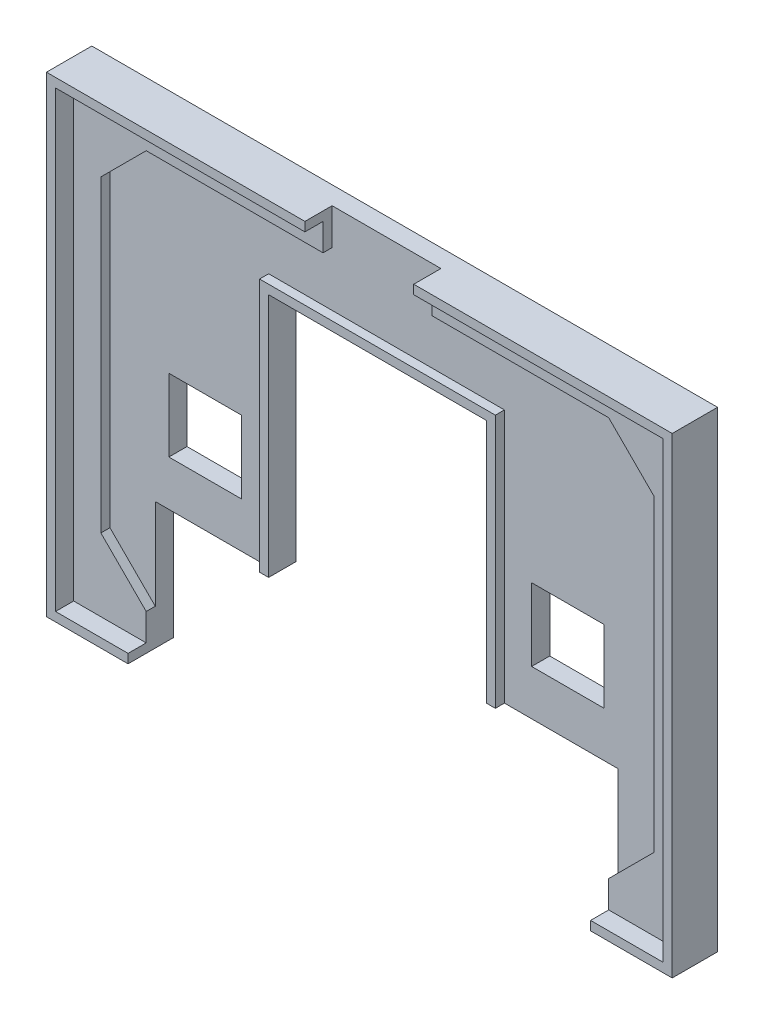
SolidWorks part; units mm, degrees
ref_plane "Přední rovina" through (0, 0, 0) normal (0, 0, 1) x (1, 0, 0)
ref_plane "Horní rovina" through (0, 0, 0) normal (0, 1, 0) x (1, 0, 0)
ref_plane "Pravá rovina" through (0, 0, 0) normal (1, 0, 0) x (0, 0, -1)
sketch "Skica1" plane through (0, 0, 0) normal (0, 0, 1) x (1, 0, 0)
  line L1 (-33.5, -25) -> (33.5, -25)
  line L2 (-33.5, -25) -> (-33.5, 25)
  line L3 (-33.5, 25) -> (33.5, 25)
  line L4 (33.5, -25) -> (33.5, 25)
  line L5 (-33.5, -25) -> (33.5, 25) construction
  line L6 (-33.5, 25) -> (33.5, -25) construction
  point P0 (0, 0)
  dimension "D1" = 67
  dimension "D2" = 50
extrude "Přidat vysunutím1" add sketch "Skica1" along normal blind 3
sketch "Skica2" plane through (0, 0, 3) normal (0, 0, 1) x (1, 0, 0)
  line L0 (-1000, 0) -> (49000, 0) construction
  line L1 (0, -1000) -> (0, 49000) construction
  line L2 (-1000, -22) -> (49000, -22) construction
  line L3 (-25.5, -1000) -> (-25.5, 49000) construction
  line L4 (-30.5, -1000) -> (-30.5, 49000) construction
  line L6 (-33.5, -25) -> (33.5, -25) construction
  line L7 (-25.5, -22) -> (-30.5, -17)
  line L8 (-30.5, -17) -> (-30.5, 17)
  line L9 (-25.5, -22) -> (25.5, -22)
  line L10 (30.5, -17) -> (30.5, 17)
  line L11 (25.5, -22) -> (30.5, -17)
  line L12 (25.5, 22) -> (30.5, 17)
  line L13 (-25.5, 22) -> (25.5, 22)
  line L14 (-25.5, 22) -> (-30.5, 17)
  point P20 (0, -22)
  point P21 (30.5, 0)
  point P24 (-30.5, 0)
  dimension "D1" = 30.5
  dimension "D2" = 5
  dimension "D3" = 3
  dimension "D4" = 45
extrude "Odebrat vysunutím1" cut sketch "Skica2" against normal offset from surface (1 mm away) 2 up to face at (0, 0, 0)
sketch "Skica3" plane through (0, 0, 0) normal (0, 0, -1) x (-1, 0, 0)
  line L0 (0, -1000) -> (0, 49000) construction
  line L1 (33.5, -25) -> (-33.5, -25) construction
  line L2 (24, 1) -> (16, 1)
  line L3 (24, 1) -> (24, -7)
  line L4 (24, -7) -> (16, -7)
  line L5 (16, 1) -> (16, -7)
  line L6 (-16, 1) -> (-16, -7)
  line L7 (33.5, -25) -> (-33.5, -25) construction
  line L8 (25.5, -25) -> (-25.5, -25)
  line L9 (25.5, -25) -> (25.5, -12)
  line L11 (-25.5, -25) -> (-25.5, -12)
  line L12 (-24, -7) -> (-16, -7)
  line L13 (25.5, -12) -> (12, -12)
  line L15 (12, -12) -> (12, 15)
  line L16 (12, 15) -> (-12, 15)
  line L17 (-12, -12) -> (-12, 15)
  line L18 (-12, -12) -> (-25.5, -12)
  line L19 (-24, 1) -> (-24, -7)
  line L20 (-24, 1) -> (-16, 1)
  dimension "D1" = 16
  dimension "D2" = 8
  dimension "D3" = 18
  dimension "D4" = 13
  dimension "D5" = 51
  dimension "D6" = 24
  dimension "D7" = 27
extrude "Odebrat vysunutím2" cut sketch "Skica3" against normal through all
sketch "Skica4" plane through (0, 0, 2) normal (0, 0, 1) x (1, 0, 0)
  line L0 (12, 15) -> (12, -12) construction
  line L1 (-12, -12) -> (-12, 15) construction
  line L2 (-12, 15) -> (12, 15) construction
  line L3 (12, 15) -> (12, -12)
  line L4 (-12, -12) -> (-12, 15)
  line L5 (-12, 15) -> (12, 15)
extrude "Vysunout tenkostěnný1" add sketch "Skica4" along normal up to surface (1 mm away) thin up to face at (0, -3.5714, 3) thin type one direction reverse wall 1
sketch "Skica5" plane through (0, 0, 0) normal (0, 0, -1) x (-1, 0, 0)
  line L0 (-33.5, 25) -> (33.5, 25) construction
  line L1 (33.5, 25) -> (33.5, -25) construction
  line L2 (33.5, -25) -> (25.5, -25) construction
  line L3 (-33.5, -25) -> (-33.5, 25) construction
  line L4 (-25.5, -25) -> (-33.5, -25) construction
  line L5 (-33.5, 25) -> (33.5, 25)
  line L6 (33.5, 25) -> (33.5, -25)
  line L7 (33.5, -25) -> (25.5, -25)
  line L8 (-33.5, -25) -> (-33.5, 25)
  line L9 (-25.5, -25) -> (-33.5, -25)
extrude "Vysunout tenkostěnný2" add sketch "Skica5" against normal blind 5 thin thin type one direction reverse wall 1
sketch "Skica6" plane through (0, 0, 2) normal (0, 0, 1) x (1, 0, 0)
  line L0 (0, -1000) -> (0, 49000) construction
  line L1 (25.5, 22) -> (-25.5, 22) construction
  line L2 (-6, 22) -> (6, 22)
  line L3 (-6, 22) -> (-6, 26)
  line L4 (-6, 26) -> (6, 26)
  line L5 (6, 22) -> (6, 26)
  line L6 (34.5, 26) -> (-34.5, 26) construction
  dimension "D1" = 12
extrude "Odebrat vysunutím3" cut sketch "Skica6" along normal through all
sketch "Skica7" plane through (0, 0, 0) normal (0, 0, -1) x (-1, 0, 0)
  line L0 (-412.4785, -204.4844) -> (-71.1451, -204.4844) construction
  line L1 (-32.44, 14.5405) -> (-23.4595, 23.94)
  line L2 (-23.4595, 23.94) -> (-14.06, 14.9595)
  line L3 (-14.06, 14.9595) -> (-23.0405, 5.56)
  line L4 (-23.0405, 5.56) -> (-32.44, 14.5405)
  line L5 (-34.5, 26) -> (34.5, 26) construction
  line L6 (0, 0) -> (0, 28.27) construction
  line L7 (-34.5, -26) -> (-34.5, 26) construction
  line L8 (14.06, 14.9595) -> (23.0405, 5.56)
  line L9 (23.4595, 23.94) -> (14.06, 14.9595)
  line L10 (32.44, 14.5405) -> (23.4595, 23.94)
  line L11 (23.0405, 5.56) -> (32.44, 14.5405)
  dimension "D1" = 13
  dimension "D2" = 13
  dimension "D3" = 2.06
  dimension "D4" = 2.06
  dimension "D5" = 2.06
extrude "Odebrat vysunutím5" cut sketch "Skica7" against normal blind 1
sketch "Skica8" plane through (0, 0, 0) normal (0, 0, -1) x (-1, 0, 0)
  line L0 (-29.2669, 14.9665) -> (-27.4593, 13.2395)
  line L1 (-27.4593, 13.2395) -> (-25.7669, 15.0108)
  line L4 (-32.44, 14.5405) -> (-23.0405, 5.56) construction
  line L5 (-23.4595, 23.94) -> (-32.44, 14.5405) construction
  line L7 (-23.6268, 17.2508) -> (-21.9329, 19.0238)
  line L8 (-21.9329, 19.0238) -> (-23.7405, 20.7508)
  line L10 (-14.06, 14.9595) -> (-23.4595, 23.94) construction
  line L12 (-24.551, 9.7693) -> (-26.3586, 11.4963)
  line L13 (-26.3586, 11.4963) -> (-25.6678, 12.2194)
  line L15 (-20.1414, 18.0037) -> (-18.3338, 16.2767)
  line L16 (-32.44, 14.5405) -> (-23.0405, 5.56) construction
  line L17 (0, 0) -> (0, 27.7759) construction
  line L30 (-29.2669, 14.9665) -> (-25.7669, 15.0108)
  line L34 (-23.9408, 14.027) -> (-22.5592, 15.473)
  line L37 (-20.8322, 17.2806) -> (-20.1414, 18.0037)
  line L38 (-24.551, 9.7693) -> (-22.1332, 12.2999)
  line L39 (-22.1332, 12.2999) -> (-22.3041, 13.8463)
  line L40 (-22.3041, 13.8463) -> (-20.7516, 13.746)
  line L41 (-20.7516, 13.746) -> (-18.3338, 16.2767)
  line L42 (-25.6678, 12.2194) -> (-23.9408, 12.2194)
  line L43 (-23.9408, 12.2194) -> (-23.9408, 14.027)
  line L45 (-20.8322, 15.473) -> (-20.8322, 17.2806)
  line L46 (-22.5592, 15.473) -> (-20.8322, 15.473)
  line L47 (-23.6268, 17.2508) -> (-23.7405, 20.7508)
  line L48 (27.4593, 13.2395) -> (25.7669, 15.0108)
  line L49 (29.2669, 14.9665) -> (27.4593, 13.2395)
  line L50 (29.2669, 14.9665) -> (25.7669, 15.0108)
  line L51 (23.6268, 17.2508) -> (21.9329, 19.0238)
  line L52 (21.9329, 19.0238) -> (23.7405, 20.7508)
  line L53 (23.6268, 17.2508) -> (23.7405, 20.7508)
  line L54 (23.9408, 14.027) -> (22.5592, 15.473)
  line L55 (23.9408, 12.2194) -> (23.9408, 14.027)
  line L56 (25.6678, 12.2194) -> (23.9408, 12.2194)
  line L57 (26.3586, 11.4963) -> (25.6678, 12.2194)
  line L58 (24.551, 9.7693) -> (26.3586, 11.4963)
  line L59 (24.551, 9.7693) -> (22.1332, 12.2999)
  line L60 (22.1332, 12.2999) -> (22.3041, 13.8463)
  line L61 (22.3041, 13.8463) -> (20.7516, 13.746)
  line L62 (20.7516, 13.746) -> (18.3338, 16.2767)
  line L63 (20.1414, 18.0037) -> (18.3338, 16.2767)
  line L64 (20.8322, 17.2806) -> (20.1414, 18.0037)
  line L65 (20.8322, 15.473) -> (20.8322, 17.2806)
  line L66 (22.5592, 15.473) -> (20.8322, 15.473)
  point P22 (-18.7598, 19.4498)
  dimension "2,5" = 2.5
  dimension "D2" = 2.5
  dimension "D3" = 2
  dimension "D4" = 1
  dimension "D5" = 1
  dimension "D6" = 2
  dimension "D7" = 2.5
  dimension "D8" = 2.5
  dimension "D9" = 3.5
  dimension "D10" = 2.5
  dimension "D11" = 2.5
  dimension "D12" = 2
  dimension "D13" = 2
  dimension "D14" = 2
  dimension "D15" = 2
  dimension "D16" = 3.5
  dimension "D17" = 40
  dimension "D18" = 40
  dimension "D19" = 2.5
  dimension "D20" = 90
  dimension "D21" = 90
  dimension "D22" = 3.5
  dimension "D23" = 3.5
  dimension "D24" = 2.5
  dimension "D25" = 2.5
  dimension "D26" = 3.098
extrude "Přidat vysunutím3" add sketch "Skica8" along normal blind 1 from offset 1 offset against normal yes
sketch "Skica9" plane through (0, 0, 0) normal (0, 0, -1) x (-1, 0, 0)
  line L0 (-10.3, 23.3) -> (-7.1, 23.3)
  line L1 (-7.1, 23.3) -> (-7.1, 22.5)
  line L2 (-7.1, 22.5) -> (-6.3, 22.5)
  line L3 (-6.3, 22.5) -> (-6.3, 21.7)
  line L4 (-6.3, 21.7) -> (-7.9, 21.7)
  line L5 (-7.9, 21.7) -> (-7.9, 22.5)
  line L6 (-7.9, 22.5) -> (-9.5, 22.5)
  line L7 (-9.5, 22.5) -> (-9.5, 18.5)
  line L8 (-9.5, 18.5) -> (-7.9, 18.5)
  line L9 (-7.9, 18.5) -> (-7.9, 19.3)
  line L10 (-7.9, 19.3) -> (-8.7, 19.3)
  line L11 (-8.7, 19.3) -> (-8.7, 20.1)
  line L12 (-8.7, 20.1) -> (-6.3, 20.1)
  line L13 (-6.3, 20.1) -> (-6.3, 18.5)
  line L14 (-6.3, 18.5) -> (-7.1, 18.5)
  line L15 (-7.1, 18.5) -> (-7.1, 17.7)
  line L16 (-7.1, 17.7) -> (-10.3, 17.7)
  line L17 (-10.3, 17.7) -> (-10.3, 18.5)
  line L18 (-10.3, 18.5) -> (-11.1, 18.5)
  line L19 (-11.1, 18.5) -> (-11.1, 22.5)
  line L20 (-11.1, 22.5) -> (-10.3, 22.5)
  line L21 (-10.3, 22.5) -> (-10.3, 23.3)
  line L22 (-5.3, 23.3) -> (-1.3, 23.3)
  line L23 (-1.3, 23.3) -> (-1.3, 22.3)
  line L24 (-1.3, 22.3) -> (-4, 22.3)
  line L25 (-4, 22.3) -> (-4, 21)
  line L26 (-4, 21) -> (-2.4, 21)
  line L27 (-2.4, 21) -> (-2.4, 20)
  line L28 (-2.4, 20) -> (-4, 20)
  line L29 (-4, 20) -> (-4, 18.7)
  line L30 (-4, 18.7) -> (-1.3, 18.7)
  line L31 (-1.3, 18.7) -> (-1.3, 17.7)
  line L32 (-1.3, 17.7) -> (-5.3, 17.7)
  line L33 (-5.3, 17.7) -> (-5.3, 23.3)
  line L34 (-0.3, 23.3) -> (1.3, 23.3)
  line L35 (1.3, 23.3) -> (1.3, 22.5)
  line L36 (1.3, 22.5) -> (2.1, 22.5)
  line L37 (2.1, 22.5) -> (2.1, 21.7)
  line L38 (2.1, 21.7) -> (2.9, 21.7)
  line L39 (2.9, 21.7) -> (2.9, 22.5)
  line L40 (2.9, 22.5) -> (3.7, 22.5)
  line L43 (5.3, 23.3) -> (5.3, 17.7)
  line L44 (5.3, 17.7) -> (3.7, 17.7)
  line L45 (3.7, 17.7) -> (3.7, 20.7)
  line L46 (3.7, 20.7) -> (2.9, 20.7)
  line L47 (2.9, 20.7) -> (2.9, 19.9)
  line L48 (2.9, 19.9) -> (2.1, 19.9)
  line L49 (2.1, 19.9) -> (2.1, 20.7)
  line L50 (2.1, 20.7) -> (1.3, 20.7)
  line L51 (1.3, 20.7) -> (1.3, 17.7)
  line L52 (1.3, 17.7) -> (-0.3, 17.7)
  line L53 (-0.3, 17.7) -> (-0.3, 23.3)
  line L54 (7.1, 23.3) -> (10.3, 23.3)
  line L55 (10.3, 23.3) -> (10.3, 22.5)
  line L56 (10.3, 22.5) -> (11.1, 22.5)
  line L57 (11.1, 22.5) -> (11.1, 18.5)
  line L58 (11.1, 18.5) -> (10.3, 18.5)
  line L59 (10.3, 18.5) -> (10.3, 17.7)
  line L60 (10.3, 17.7) -> (7.1, 17.7)
  line L61 (7.1, 17.7) -> (7.1, 18.5)
  line L62 (7.1, 18.5) -> (6.3, 18.5)
  line L63 (6.3, 18.5) -> (6.3, 22.5)
  line L64 (6.3, 22.5) -> (7.1, 22.5)
  line L65 (7.1, 22.5) -> (7.1, 23.3)
  line L66 (-12, 15) -> (-12, -12) construction
  line L67 (-34.5, 26) -> (34.5, 26) construction
  line L69 (3.7, 22.5) -> (3.7, 23.3)
  line L70 (3.7, 23.3) -> (5.3, 23.3)
  dimension "D1" = 3.2
  dimension "D2" = 0.8
  dimension "D3" = 0.8
  dimension "D4" = 0.8
  dimension "D5" = 0.8
  dimension "D6" = 0.8
  dimension "D7" = 5.6
  dimension "D8" = 0.8
  dimension "D9" = 0.8
  dimension "D10" = 3.2
  dimension "D11" = 0.8
  dimension "D12" = 0.8
  dimension "D13" = 1.6
  dimension "D14" = 0.8
  dimension "D15" = 2.4
  dimension "D16" = 0.8
  dimension "D17" = 0.8
  dimension "D18" = 0.9
  dimension "D19" = 2.7
  dimension "D20" = 1.6
  dimension "D21" = 0.8
  dimension "D22" = 1.6
  dimension "D23" = 4
  dimension "D24" = 4
  dimension "D25" = 1
  dimension "D26" = 1.3
  dimension "D27" = 1.3
  dimension "D28" = 1
  dimension "D29" = 1.3
  dimension "D30" = 1
  dimension "D31" = 1
  dimension "D32" = 1.6
  dimension "D33" = 1.6
  dimension "D34" = 0.8
  dimension "D35" = 0
  dimension "D36" = 0.8
  dimension "D37" = 0.8
  dimension "D38" = 1.6
  dimension "D39" = 1.6
  dimension "D40" = 1.6
  dimension "D41" = 1
  dimension "D42" = 1
  dimension "D43" = 0.8
  dimension "D44" = 0.8
  dimension "D45" = 0.8
  dimension "D46" = 0.8
  dimension "D47" = 0.8
  dimension "D48" = 0.8
  dimension "D49" = 0.8
  dimension "D50" = 3
  dimension "D51" = 3
  dimension "D52" = 0.8
  dimension "D53" = 0.8
  dimension "D54" = 3.2
  dimension "D55" = 3.2
  dimension "D56" = 0.8
  dimension "D57" = 0.8
  dimension "D58" = 0.8
  dimension "D59" = 0.8
  dimension "D60" = 0.8
extrude "Odebrat vysunutím6" cut sketch "Skica9" against normal blind 1
sketch "Skica10" plane through (0, 0, 1) normal (0, 0, -1) x (-1, 0, 0)
  line L0 (10.3, 23.3) -> (7.1, 23.3) construction
  line L1 (7.9, 21.7) -> (9.5, 21.7)
  line L2 (7.9, 21.7) -> (7.9, 19.3)
  line L3 (7.9, 19.3) -> (9.5, 19.3)
  line L4 (9.5, 21.7) -> (9.5, 19.3)
  line L5 (6.3, 22.5) -> (6.3, 18.5) construction
  line L6 (7.1, 17.7) -> (10.3, 17.7) construction
  line L7 (11.1, 18.5) -> (11.1, 22.5) construction
  dimension "D1" = 1.6
  dimension "D2" = 1.6
  dimension "D3" = 1.6
  dimension "D4" = 1.6
extrude "Přidat vysunutím4" add sketch "Skica10" along normal blind 1
